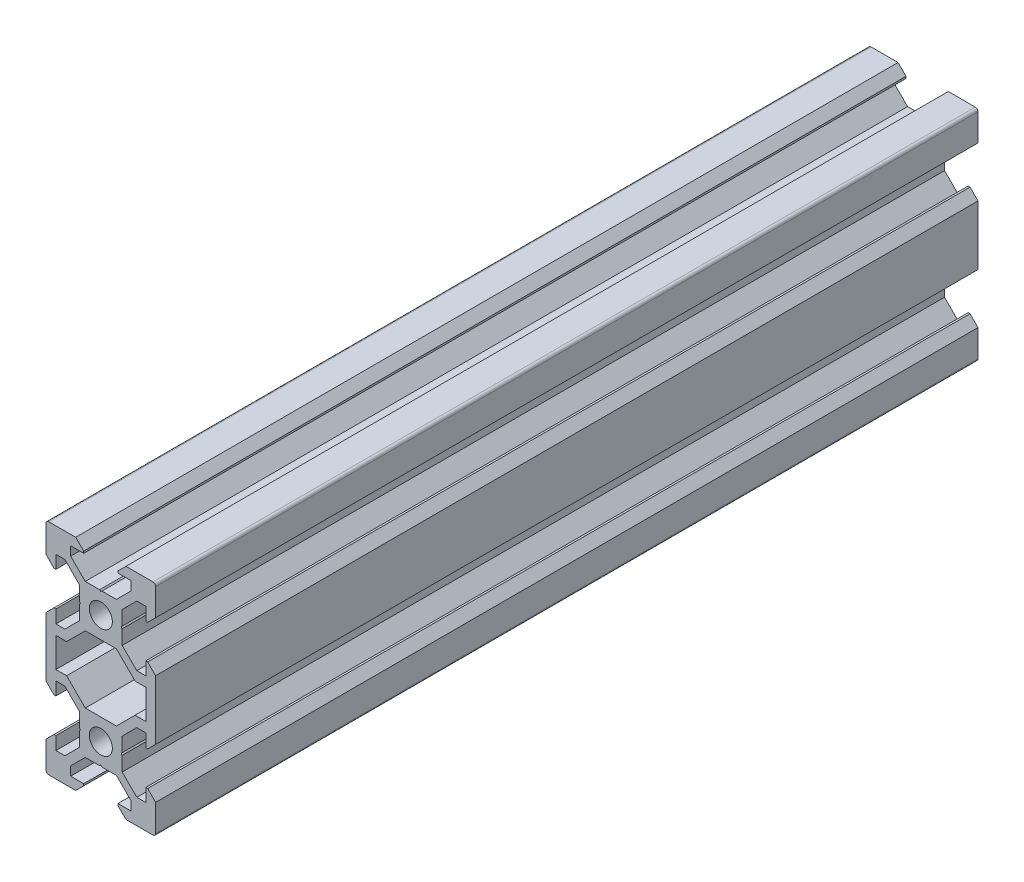
SolidWorks part; units mm, degrees
material "6061-T6 (SS)"
ref_plane "Front Plane" through (0, 0, 0) normal (0, 0, 1) x (1, 0, 0)
ref_plane "Top Plane" through (0, 0, 0) normal (0, 1, 0) x (1, 0, 0)
ref_plane "Right Plane" through (0, 0, 0) normal (1, 0, 0) x (0, 0, -1)
sketch "Sketch1" plane through (0, 0, 0) normal (0, 0, 1) x (1, 0, 0)
  line L0 (0, 0) -> (10, 0) construction
  line L1 (9.5, -20) -> (-9.5, -20)
  line L2 (10, -19.5) -> (10, 19.5)
  line L3 (9.5, 20) -> (-9.5, 20)
  line L4 (-10, -19.5) -> (-10, 19.5)
  line L5 (10, -20) -> (-10, 20) construction
  line L6 (10, 20) -> (-10, -20) construction
  circle A0 centre (0, 10) radius 2.1
  circle A1 centre (0, -10) radius 2.1
  arc A2 (-9.5, -20) -> (-10, -19.5) centre (-9.5, -19.5) cw
  arc A3 (9.5, -20) -> (10, -19.5) centre (9.5, -19.5) ccw
  arc A4 (10, 19.5) -> (9.5, 20) centre (9.5, 19.5) ccw
  arc A5 (-9.5, 20) -> (-10, 19.5) centre (-9.5, 19.5) ccw
  point P0 (0, 0)
  line B0 (0, 10) -> (0, 20) construction
  line B1 (0, 13.69) -> (-0.21, 13.9)
  line B2 (-0.21, 13.9) -> (-2.8393, 13.9)
  line B3 (-2.8393, 13.9) -> (-5.5, 16.5607)
  line B4 (-5.5, 16.5607) -> (-5.5, 18.2)
  line B5 (-5.5, 18.2) -> (-3.125, 18.2)
  line B6 (-3.125, 18.2) -> (-3.125, 18.545)
  line B7 (-3.125, 18.545) -> (-4.58, 20)
  line B8 (-4.58, 20) -> (4.58, 20)
  line B9 (0, 10) -> (-5.9132, 15.9132) construction
  line B10 (3.125, 18.545) -> (4.58, 20)
  line B11 (3.125, 18.2) -> (3.125, 18.545)
  line B12 (5.5, 18.2) -> (3.125, 18.2)
  line B13 (5.5, 16.5607) -> (5.5, 18.2)
  line B14 (2.8393, 13.9) -> (5.5, 16.5607)
  line B15 (0.21, 13.9) -> (2.8393, 13.9)
  line B16 (0, 13.69) -> (0.21, 13.9)
  line B17 (0, 10) -> (-10, 10) construction
  line B18 (-3.69, 10) -> (-3.9, 9.79)
  line B19 (-3.9, 9.79) -> (-3.9, 7.1607)
  line B20 (-3.9, 7.1607) -> (-6.5607, 4.5)
  line B21 (-6.5607, 4.5) -> (-8.2, 4.5)
  line B22 (-8.2, 4.5) -> (-8.2, 6.875)
  line B23 (-8.2, 6.875) -> (-8.545, 6.875)
  line B24 (-8.545, 6.875) -> (-10, 5.42)
  line B25 (-10, 5.42) -> (-10, 14.58)
  line B26 (0, 10) -> (-5.9132, 4.0868) construction
  line B27 (-8.545, 13.125) -> (-10, 14.58)
  line B28 (-8.2, 13.125) -> (-8.545, 13.125)
  line B29 (-8.2, 15.5) -> (-8.2, 13.125)
  line B30 (-6.5607, 15.5) -> (-8.2, 15.5)
  line B31 (-3.9, 12.8393) -> (-6.5607, 15.5)
  line B32 (-3.9, 10.21) -> (-3.9, 12.8393)
  line B33 (-3.69, 10) -> (-3.9, 10.21)
  line B34 (0, -10) -> (-10, -10) construction
  line B35 (-3.69, -10) -> (-3.9, -10.21)
  line B36 (-3.9, -10.21) -> (-3.9, -12.8393)
  line B37 (-3.9, -12.8393) -> (-6.5607, -15.5)
  line B38 (-6.5607, -15.5) -> (-8.2, -15.5)
  line B39 (-8.2, -15.5) -> (-8.2, -13.125)
  line B40 (-8.2, -13.125) -> (-8.545, -13.125)
  line B41 (-8.545, -13.125) -> (-10, -14.58)
  line B42 (-10, -14.58) -> (-10, -5.42)
  line B43 (0, -10) -> (-5.9132, -15.9132) construction
  line B44 (-8.545, -6.875) -> (-10, -5.42)
  line B45 (-8.2, -6.875) -> (-8.545, -6.875)
  line B46 (-8.2, -4.5) -> (-8.2, -6.875)
  line B47 (-6.5607, -4.5) -> (-8.2, -4.5)
  line B48 (-3.9, -7.1607) -> (-6.5607, -4.5)
  line B49 (-3.9, -9.79) -> (-3.9, -7.1607)
  line B50 (-3.69, -10) -> (-3.9, -9.79)
  line B51 (0, -10) -> (0, -20) construction
  line B52 (0, -13.69) -> (0.21, -13.9)
  line B53 (0.21, -13.9) -> (2.8393, -13.9)
  line B54 (2.8393, -13.9) -> (5.5, -16.5607)
  line B55 (5.5, -16.5607) -> (5.5, -18.2)
  line B56 (5.5, -18.2) -> (3.125, -18.2)
  line B57 (3.125, -18.2) -> (3.125, -18.545)
  line B58 (3.125, -18.545) -> (4.58, -20)
  line B59 (4.58, -20) -> (-4.58, -20)
  line B60 (0, -10) -> (5.9132, -15.9132) construction
  line B61 (-3.125, -18.545) -> (-4.58, -20)
  line B62 (-3.125, -18.2) -> (-3.125, -18.545)
  line B63 (-5.5, -18.2) -> (-3.125, -18.2)
  line B64 (-5.5, -16.5607) -> (-5.5, -18.2)
  line B65 (-2.8393, -13.9) -> (-5.5, -16.5607)
  line B66 (-0.21, -13.9) -> (-2.8393, -13.9)
  line B67 (0, -13.69) -> (-0.21, -13.9)
  line B68 (0, -10) -> (10, -10) construction
  line B69 (3.69, -10) -> (3.9, -9.79)
  line B70 (3.9, -9.79) -> (3.9, -7.1607)
  line B71 (3.9, -7.1607) -> (6.5607, -4.5)
  line B72 (6.5607, -4.5) -> (8.2, -4.5)
  line B73 (8.2, -4.5) -> (8.2, -6.875)
  line B74 (8.2, -6.875) -> (8.545, -6.875)
  line B75 (8.545, -6.875) -> (10, -5.42)
  line B76 (10, -5.42) -> (10, -14.58)
  line B77 (0, -10) -> (5.9132, -4.0868) construction
  line B78 (8.545, -13.125) -> (10, -14.58)
  line B79 (8.2, -13.125) -> (8.545, -13.125)
  line B80 (8.2, -15.5) -> (8.2, -13.125)
  line B81 (6.5607, -15.5) -> (8.2, -15.5)
  line B82 (3.9, -12.8393) -> (6.5607, -15.5)
  line B83 (3.9, -10.21) -> (3.9, -12.8393)
  line B84 (3.69, -10) -> (3.9, -10.21)
  line B85 (0, 10) -> (10, 10) construction
  line B86 (3.69, 10) -> (3.9, 10.21)
  line B87 (3.9, 10.21) -> (3.9, 12.8393)
  line B88 (3.9, 12.8393) -> (6.5607, 15.5)
  line B89 (6.5607, 15.5) -> (8.2, 15.5)
  line B90 (8.2, 15.5) -> (8.2, 13.125)
  line B91 (8.2, 13.125) -> (8.545, 13.125)
  line B92 (8.545, 13.125) -> (10, 14.58)
  line B93 (10, 14.58) -> (10, 5.42)
  line B94 (0, 10) -> (5.9132, 15.9132) construction
  line B95 (8.545, 6.875) -> (10, 5.42)
  line B96 (8.2, 6.875) -> (8.545, 6.875)
  line B97 (8.2, 4.5) -> (8.2, 6.875)
  line B98 (6.5607, 4.5) -> (8.2, 4.5)
  line B99 (3.9, 7.1607) -> (6.5607, 4.5)
  line B100 (3.9, 9.79) -> (3.9, 7.1607)
  line B101 (3.69, 10) -> (3.9, 9.79)
  line B102 (-8.2, -2.7) -> (-8.2, 2.7)
  line B103 (-8.2, 2.7) -> (-6.2393, 2.7)
  line B104 (-6.2393, 2.7) -> (-2.8393, 6.1)
  line B105 (-2.8393, 6.1) -> (2.8393, 6.1)
  line B106 (0, 6.1) -> (0, 0) construction
  line B107 (0, 0) -> (-8.2, 0) construction
  line B108 (6.2393, 2.7) -> (2.8393, 6.1)
  line B109 (8.2, 2.7) -> (6.2393, 2.7)
  line B110 (8.2, -2.7) -> (8.2, 2.7)
  line B111 (8.2, -2.7) -> (6.2393, -2.7)
  line B112 (6.2393, -2.7) -> (2.8393, -6.1)
  line B113 (-2.8393, -6.1) -> (2.8393, -6.1)
  line B114 (-6.2393, -2.7) -> (-2.8393, -6.1)
  line B115 (-8.2, -2.7) -> (-6.2393, -2.7)
  line B116 (0, 6.1) -> (0, 10) construction
  line B117 (0, 10) -> (-5.0927, 4.9073) construction
  dimension "D4" = 4.2
  dimension "D5" = 0.5
  dimension "D1" = 20
  dimension "D2" = 40
  dimension "D3" = 20
sketch_block_instance "V Slot 1-4"
sketch_block "V Slot 1" parameters "D1"=10, "D2"=11, "D3"=4.3, "D4"=1.8, "D5"=0.21, "D6"=45, "D7"=9.16, "D8"=1.5, "D9"=6.25
sketch_block_instance "V Slot 1-5"
sketch_block_instance "V Slot 1-6"
sketch_block_instance "V Slot 1-7"
sketch_block_instance "V Slot 1-8"
sketch_block_instance "V Slot 1-9"
sketch_block_instance "Center Cutout 1-1"
sketch_block "Center Cutout 1" parameters "D1"=5.4, "D2"=12.2, "D3"=8.2, "D4"=45, "D5"=10, "D6"=1.5
extrude "Boss-Extrude1" add sketch "Sketch1" along normal blind 150 contours B101 B86 B87 B88 B89 B90 B91 B92 L2 A4 L3 B10 B11 B12 B13 B14 B15 B16 B1 B2 B3 B4 B5 B6 B7 A5 L4 B27 B28 B29 B30 B31 B32 B33 B18 B19 B20 B21 B22 B23 B24 B44 B45 B46 B47 B48 B49 B50 B35
